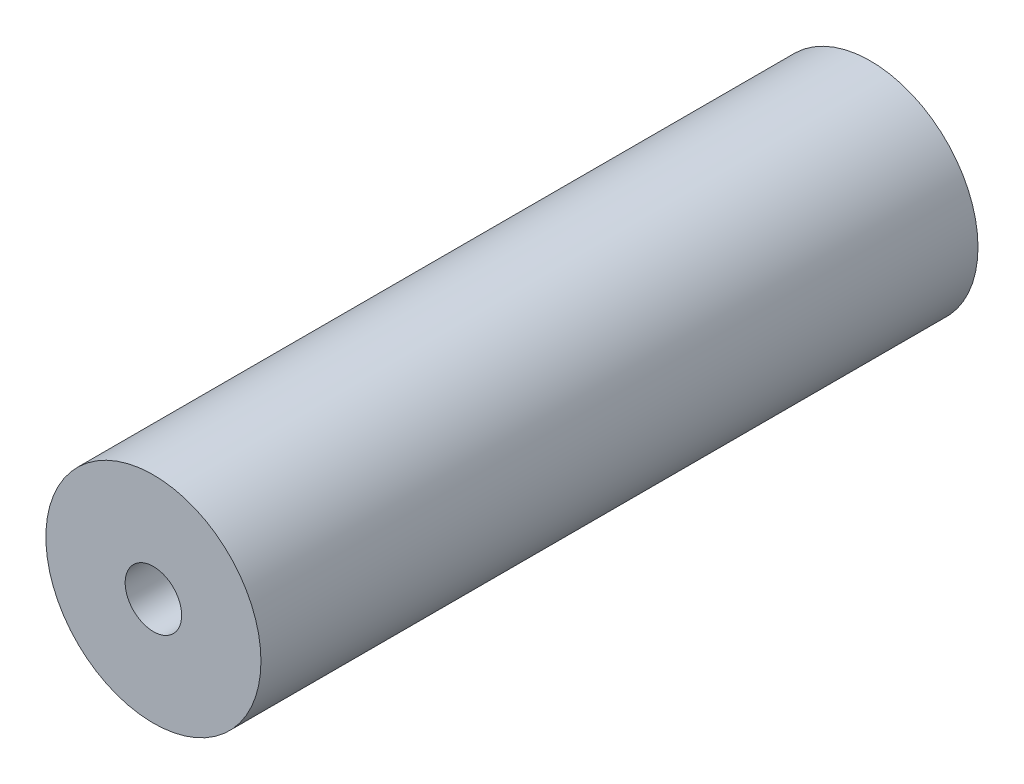
SolidWorks part; units mm, degrees
material "6061-T6 (SS)"
ref_plane "Front Plane" through (0, 0, 0) normal (0, 0, 1) x (1, 0, 0)
ref_plane "Top Plane" through (0, 0, 0) normal (0, 1, 0) x (1, 0, 0)
ref_plane "Right Plane" through (0, 0, 0) normal (1, 0, 0) x (0, 0, -1)
sketch "Sketch1" plane through (0, 0, 0) normal (0, 0, 1) x (1, 0, 0)
  circle A0 centre (0, 0) radius 9.525
  dimension "D1" = 19.05
extrude "Boss-Extrude1" add sketch "Sketch1" along normal mid plane 63.5
hole_wizard "M6x1.0 Tapped Hole1" positions "Sketch3" profile "Sketch2" tap size "M6x1.0" standard "ANSI Metric"
sketch "Sketch3" plane through (0, 0, 31.75) normal (0, 0, 1) x (1, 0, 0)
  point P0 (0, 0)
sketch "Sketch2" plane through (0, 0, 31.75) normal (1, 0, 0) x (0, -1, 0)
  line L0 (0, 0) -> (0, 16.5136)
  line L1 (0, 16.5136) -> (2.5, 15.0114)
  line L2 (2.5, 15.0114) -> (2.5, 0)
  line L5 (2.5, 0) -> (0, 0)
  line L10 (0, 16.5136) -> (-2.5, 15.0114) construction
  line L11 (0, -6.35) -> (0, 107.95) construction
  dimension "Tap Drill Dia." = 5
  dimension "Tap Drill Depth" = 15.0114
  dimension "Drill Angle" = 118
cosmetic thread "Hole Thread1" parameters "D1"=11.9888, "D2"=6
hole_wizard "M6x1.0 Tapped Hole2" positions "Sketch5" profile "Sketch4" tap size "M6x1.0" standard "ANSI Metric"
sketch "Sketch5" plane through (0, 0, -31.75) normal (0, 0, -1) x (-1, 0, 0)
  point P0 (0, 0)
sketch "Sketch4" plane through (0, 0, -31.75) normal (1, 0, 0) x (0, 1, 0)
  line L0 (0, 0) -> (0, 16.5136)
  line L1 (0, 16.5136) -> (2.5, 15.0114)
  line L2 (2.5, 15.0114) -> (2.5, 0)
  line L5 (2.5, 0) -> (0, 0)
  line L10 (0, 16.5136) -> (-2.5, 15.0114) construction
  line L11 (0, -6.35) -> (0, 107.95) construction
  dimension "Tap Drill Dia." = 5
  dimension "Tap Drill Depth" = 15.0114
  dimension "Drill Angle" = 118
cosmetic thread "Hole Thread2"
